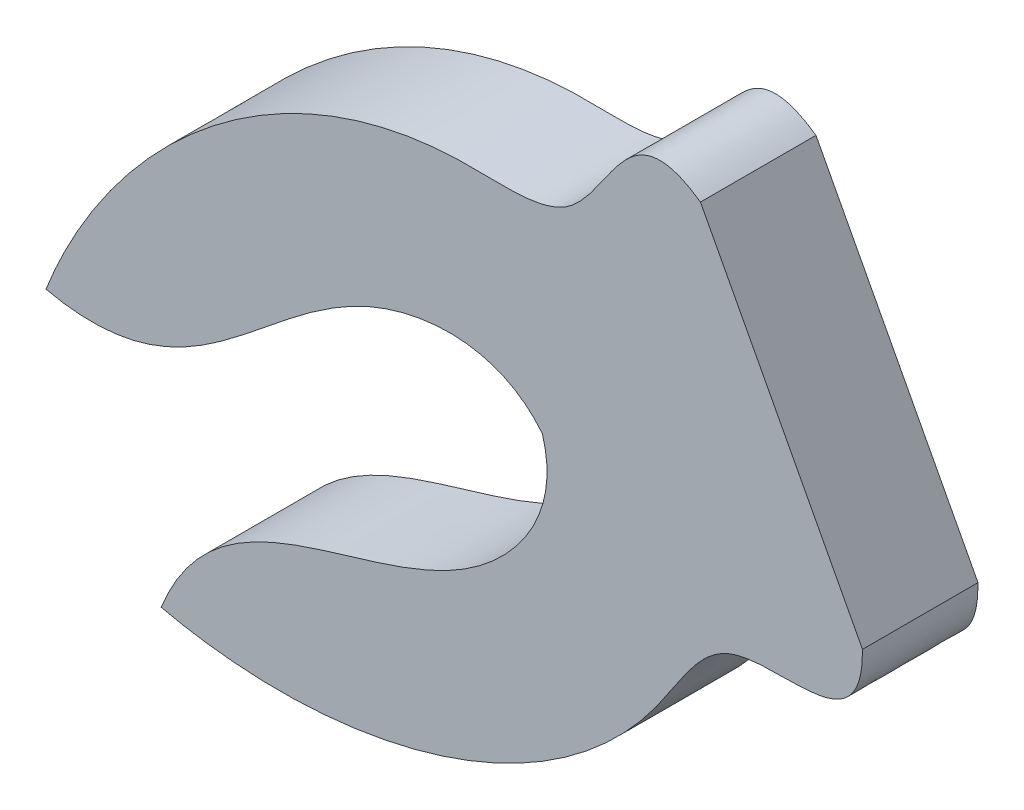
SolidWorks part; units mm, degrees
ref_plane "Front Plane" through (0, 0, 0) normal (0, 0, 1) x (1, 0, 0)
ref_plane "Top Plane" through (0, 0, 0) normal (0, 1, 0) x (1, 0, 0)
ref_plane "Right Plane" through (0, 0, 0) normal (1, 0, 0) x (0, 0, -1)
sketch "Sketch1" plane through (0, 0, 0) normal (0, 0, 1) x (1, 0, 0)
  line L0 (221.4168, 256.1847) -> (1107.0838, 256.1847) construction
  line L1 (184.1709, 171.1644) -> (188.6238, 162.7444)
  line L2 (186.3974, 166.9544) -> (169.5573, 158.0486)
  spline S0 degree 3 poles (184.1709, 171.1644) (182.1205, 172.609) (181.4979, 168.5041) (173.1984, 169.5742) (167.9478, 164.6147) (166.184, 160.0951) knots 0 0 0 0 0.2073 0.334319 1 1 1 1
  spline S1 degree 3 poles (166.184, 160.0951) (170.3866, 159.1581) (172.8706, 164.7937) (178.7455, 164.8257) (179.8262, 163.4793) knots 0 0 0 0 0.681894 1 1 1 1
  spline S2 degree 3 poles (188.6238, 162.7444) (188.6636, 160.2366) (184.9203, 162.0326) (181.1331, 154.5704) (174.0784, 153.0223) (169.3499, 154.1085) knots 0 0 0 0 0.2073 0.334319 1 1 1 1
  spline S3 degree 3 poles (169.3499, 154.1085) (170.9411, 158.1095) (176.9974, 156.9904) (180.3307, 161.8281) (179.8262, 163.4793) knots 0 0 0 0 0.681894 1 1 1 1
  dimension "D2" = 19.05
  dimension "D1" = 9.525
extrude "Boss-Extrude1" add sketch "Sketch1" along normal blind 3.175 contours L1 S2 S3 S1 S0
